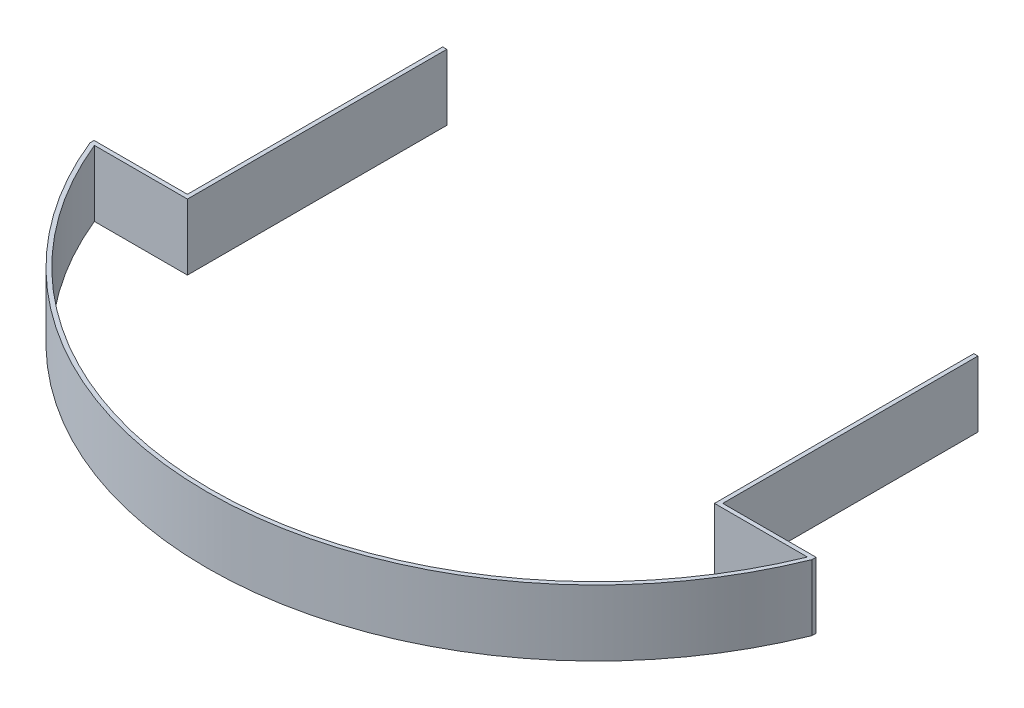
SolidWorks part; units mm, degrees
ref_plane "Front Plane" through (0, 0, 0) normal (0, 0, 1) x (1, 0, 0)
ref_plane "Top Plane" through (0, 0, 0) normal (0, 1, 0) x (1, 0, 0)
ref_plane "Right Plane" through (0, 0, 0) normal (1, 0, 0) x (0, 0, -1)
sketch "Sketch1" plane through (0, 0, 0) normal (0, 1, 0) x (1, 0, 0)
  line L0 (-101.6, -56) -> (-139.1546, -56)
  line L1 (-101.6, 56) -> (101.6, 56)
  line L2 (-101.6, 56) -> (-101.6, -56)
  line L3 (-101.6, -56) -> (101.6, -56)
  line L4 (101.6, 56) -> (101.6, -56)
  line L5 (-101.6, 56) -> (101.6, -56) construction
  line L6 (-101.6, -56) -> (101.6, 56) construction
  line L7 (101.6, -56) -> (139.1546, -56)
  line L9 (-139.1546, -56) -> (-101.6, -56)
  line L10 (-139.1546, -56) -> (-139.1546, -54.4125)
  line L11 (-139.1546, -54.4125) -> (-101.6, -54.4125)
  line L12 (-101.6, -56) -> (-101.6, -54.4125)
  line L13 (-101.6, -56) -> (-103.188, -56)
  line L14 (-101.6, -56) -> (-101.6, 44)
  line L15 (-101.6, 44) -> (-103.188, 44)
  line L16 (-103.188, -56) -> (-103.188, 44)
  line L17 (139.1546, -56) -> (101.6, -56)
  line L18 (139.1546, -56) -> (139.1546, -54.412)
  line L19 (139.1546, -54.412) -> (101.6, -54.412)
  line L20 (101.6, -56) -> (101.6, -54.412)
  line L21 (101.6, -56) -> (103.188, -56)
  line L22 (101.6, -56) -> (101.6, 44)
  line L23 (101.6, 44) -> (103.188, 44)
  line L24 (103.188, -56) -> (103.188, 44)
  circle A0 centre (0, 0) radius 148.412
  circle A1 centre (0, 0) radius 150
  point P0 (0, 0)
  dimension "D3" = 1.588
  dimension "D1" = 203.2
  dimension "D2" = 112
  dimension "D4" = 1.5875
  dimension "D5" = 1.588
  dimension "D6" = 1.588
  dimension "D7" = 1.588
  dimension "D8" = 100
  dimension "D9" = 100
extrude "Boss-Extrude1" add sketch "Sketch1" along normal blind 25.4 contours L0 A1 L7 A0 | L17 A0 L19 L24 | L7 L24 L19 L4 | L19 L24 L23 L4 | L16 L11 L2 L15 | L16 L0 L2 L11 | L11 A0 L9 L16 | A0 L11 L10 L0 | A0 L7 L18 L19
